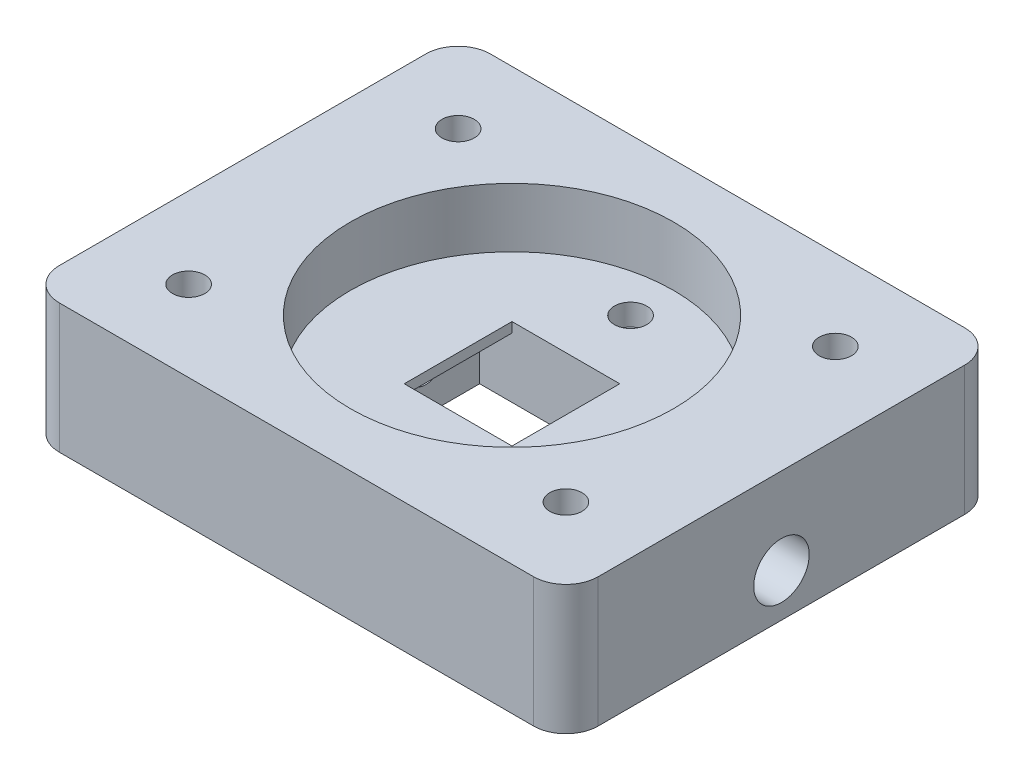
SolidWorks part; units mm, degrees
other "BodyCell"
ref_plane "Front Plane" through (0, 0, 0) normal (0, 0, 1) x (1, 0, 0)
ref_plane "Top Plane" through (0, 0, 0) normal (0, 1, 0) x (1, 0, 0)
ref_plane "Right Plane" through (0, 0, 0) normal (1, 0, 0) x (0, 0, -1)
sketch "Sketch1" plane through (0, 0, 0) normal (0, 1, 0) x (1, 0, 0)
  line L1 (25, -20) -> (-25, -20)
  line L2 (25, -20) -> (25, 20)
  line L3 (25, 20) -> (-25, 20)
  line L4 (-25, -20) -> (-25, 20)
  line L5 (25, -20) -> (-25, 20) construction
  line L6 (25, 20) -> (-25, -20) construction
  point P0 (0, 0)
  dimension "D1" = 50
  dimension "D2" = 40
extrude "Body" add sketch "Sketch1" along normal blind 12
fillet "FilletBody" radius 3 4 edges at (-25, 6, -20) (25, 6, -20) (25, 6, 20) (-25, 6, 20)
sketch "Sketch3" plane through (0, 12, 0) normal (0, 1, 0) x (1, 0, 0)
  line L0 (-25, 17) -> (-25, -17) construction
  line L1 (22, 20) -> (-22, 20) construction
  line L2 (-38.934, 0) -> (38.0552, 0) construction
  line L3 (0, 29.5616) -> (0, -31.3312) construction
  circle A0 centre (-17.5, 12.5) radius 1.5
  circle A1 centre (17.5, 12.5) radius 1.5
  circle A2 centre (17.5, -12.5) radius 1.5
  circle A3 centre (-17.5, -12.5) radius 1.5
  dimension "D1" = 3
  dimension "D2" = 7.5
  dimension "D3" = 7.5
sketch "Sketch41" plane through (-25, 0, 0) normal (-1, 0, 0) x (0, 0, 1)
  line L0 (0, -55) -> (0, 55) construction
  line L1 (55, 0) -> (-55, 0) construction
  circle A0 centre (0, 4) radius 1.575
  dimension "D1" = 3.15
  dimension "D2" = 4
extrude "Channel1" cut sketch "Sketch41" against normal blind 57
sketch "Sketch42" plane through (-25, 0, 0) normal (-1, 0, 0) x (0, 0, 1)
  circle A0 centre (0, 4) radius 2.575
  dimension "D1" = 5.15
extrude "Inlet" cut sketch "Sketch42" against normal blind 5
sketch "Sketch43" plane through (25, 0, 0) normal (1, 0, 0) x (0, 0, -1)
  circle A0 centre (0, 4) radius 2.575 construction
  circle A1 centre (0, 4) radius 2.575
extrude "Outlet" cut sketch "Sketch43" against normal blind 5
sketch "Sketch44" plane through (0, 12, 0) normal (0, 1, 0) x (1, 0, 0)
  circle A0 centre (0, 0) radius 15
  dimension "D1" = 30
extrude "Window" cut sketch "Sketch44" against normal blind 5.5
sketch "Sketch45" plane through (0, 0, 0) normal (0, -1, 0) x (1, 0, 0)
  line L1 (8, -5) -> (-8, -5)
  line L2 (8, -5) -> (8, 5)
  line L3 (8, 5) -> (-8, 5)
  line L4 (-8, -5) -> (-8, 5)
  line L5 (8, -5) -> (-8, 5) construction
  line L6 (8, 5) -> (-8, -5) construction
  point P0 (0, 0)
  dimension "D1" = 10
  dimension "D2" = 16
extrude "FlowCh" cut sketch "Sketch45" against normal blind 5.575
sketch "Sketch46" plane through (0, 6.5, 0) normal (0, 1, 0) x (1, 0, 0)
  line L1 (5, -5) -> (-5, -5)
  line L2 (5, -5) -> (5, 5)
  line L3 (5, 5) -> (-5, 5)
  line L4 (-5, -5) -> (-5, 5)
  line L5 (5, -5) -> (-5, 5) construction
  line L6 (5, 5) -> (-5, -5) construction
  point P0 (0, 0)
  dimension "D1" = 10
  dimension "D2" = 10
extrude "Window_hole" cut sketch "Sketch46" against normal blind 16
sketch "Sketch49" plane through (0, 6.5, 0) normal (0, 1, 0) x (1, 0, 0)
  line L0 (-6.6, 0) -> (6.6, 0) construction
  circle A5 centre (0, 11) radius 1.5
  circle A7 centre (0, -11) radius 1.5
  circle A9 centre (-11, 0) radius 1.5 [skipped]
  circle A10 centre (11, 0) radius 1.5 [skipped]
  point P14 (0, 0)
  dimension "D3" = 3
  dimension "D1" = 11
  dimension "D2" = 4
extrude "FixHoles" cut sketch "Sketch49" against normal blind 2
sketch "Sketch50" plane through (0, 0, 0) normal (0, -1, 0) x (1, 0, 0)
  line L0 (-8, 7) -> (8, 7)
  line L1 (8, 5) -> (-8, 5) construction
  line L2 (10, 5) -> (10, -5)
  line L3 (8, -5) -> (8, 5) construction
  line L4 (0, 12.2512) -> (0, -10.9162) construction
  line L5 (-29.6034, 0) -> (30.3234, 0) construction
  line L6 (6.6, 0) -> (-6.6, 0) construction
  line L7 (-10, 5) -> (-10, -5)
  line L8 (-8, -7) -> (8, -7)
  line L9 (14, 5) -> (14, -5)
  line L10 (-8, -11) -> (8, -11)
  line L11 (-14, 5) -> (-14, -5)
  line L12 (-8, 11) -> (8, 11)
  arc A0 (8, 7) -> (10, 5) centre (8, 5) cw
  arc A1 (-8, 7) -> (-10, 5) centre (-8, 5) ccw
  arc A2 (8, -7) -> (10, -5) centre (8, -5) ccw
  arc A3 (-8, -7) -> (-10, -5) centre (-8, -5) cw
  arc A4 (8, -11) -> (14, -5) centre (8, -5) ccw
  arc A5 (-8, -11) -> (-14, -5) centre (-8, -5) cw
  arc A6 (-8, 11) -> (-14, 5) centre (-8, 5) ccw
  arc A7 (8, 11) -> (14, 5) centre (8, 5) cw
  dimension "D1" = 2
  dimension "D2" = 2
  dimension "D3" = 4
extrude "Gasket" cut sketch "Sketch50" against normal blind 1 contours A7 L12 A6 L11 A5 L10 A4 L9 L8 A3 L7 A1 L0 A0 L2 A2
extrude "Bolt_hole" cut sketch "Sketch3" against normal blind 31 and the other way blind 10
